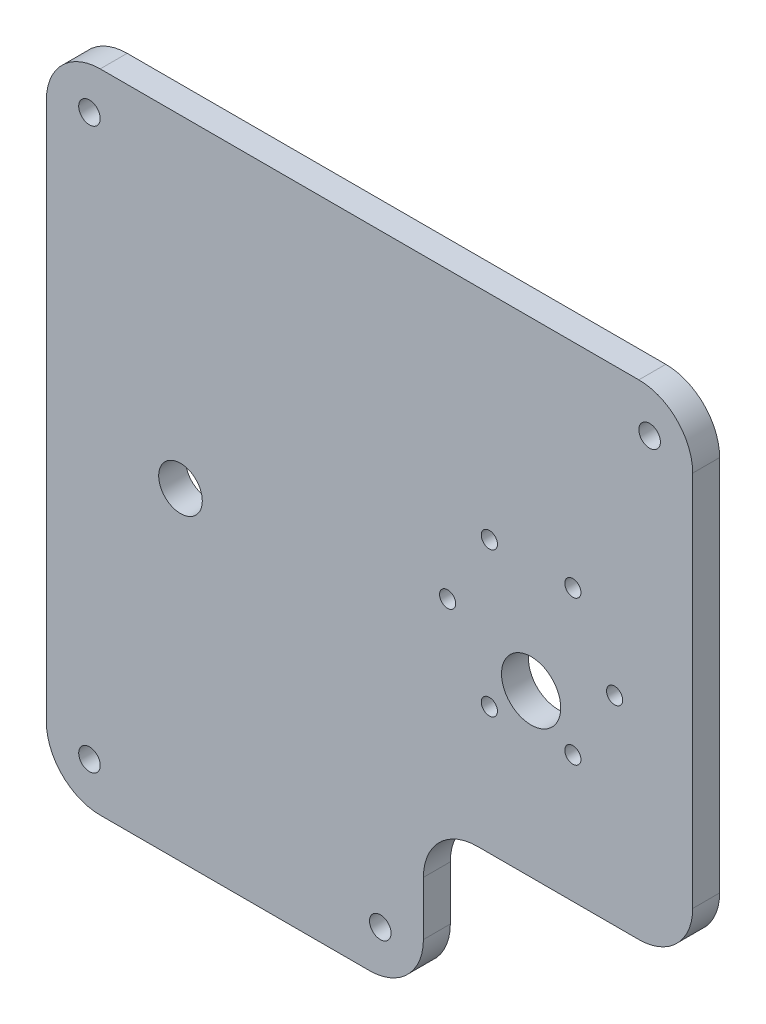
SolidWorks part; units mm, degrees
ref_plane "Alzado" through (0, 0, 0) normal (0, 0, 1) x (1, 0, 0)
ref_plane "Planta" through (0, 0, 0) normal (0, 1, 0) x (1, 0, 0)
ref_plane "Vista lateral" through (0, 0, 0) normal (1, 0, 0) x (0, 0, -1)
sketch "Croquis1" plane through (0, 0, 0) normal (0, 0, 1) x (1, 0, 0)
  line L0 (110, 30) -> (80, 30)
  line L1 (10, 0) -> (60, 0)
  line L2 (0, 10) -> (0, 110)
  line L3 (10, 120) -> (110, 120)
  line L4 (120, 40) -> (120, 110)
  line L5 (70, 20) -> (70, 10)
  arc A0 (10, 0) -> (0, 10) centre (10, 10) cw
  arc A1 (70, 10) -> (60, 0) centre (60, 10) cw
  arc A2 (110, 120) -> (120, 110) centre (110, 110) cw
  arc A3 (0, 110) -> (10, 120) centre (10, 110) cw
  arc A4 (80, 30) -> (70, 20) centre (80, 20) ccw
  arc A5 (110, 30) -> (120, 40) centre (110, 40) ccw
  point P7 (0, 0)
  point P10 (120, 0)
  point P15 (0, 120)
  dimension "D3" = 10
  dimension "D6" = 10
  dimension "D1" = 120
  dimension "D2" = 120
  dimension "D4" = 30
  dimension "D5" = 50
extrude "Saliente-Extruir1" add sketch "Croquis1" along normal blind 5
sketch "Croquis2" plane through (0, 0, 5) normal (0, 0, 1) x (1, 0, 0)
  line L0 (60, 120) -> (60, 75.4201) construction
  line L1 (110, 120) -> (10, 120) construction
  line L2 (0, 110) -> (0, 10) construction
  line L3 (0, 60) -> (90, 60) construction
  line L4 (120, 40) -> (120, 110) construction
  line L5 (70, 10) -> (70, 20) construction
  line L6 (10, 0) -> (60, 0) construction
  line L9 (90, 67) -> (90, 60) construction
  line L10 (82.25, 80.4234) -> (97.75, 53.5766) construction
  line L11 (97.75, 80.4234) -> (82.25, 53.5766) construction
  line L12 (74.5, 67) -> (105.5, 67) construction
  circle A0 centre (8, 112) radius 2
  circle A1 centre (8, 8) radius 2
  circle A2 centre (112, 8) radius 2
  circle A3 centre (112, 112) radius 2
  circle A5 centre (62, 8) radius 2
  circle A6 centre (24.9, 60) radius 4.05
  circle A8 centre (82.25, 80.4234) radius 1.5
  circle A9 centre (97.75, 80.4234) radius 1.5
  circle A10 centre (105.5, 67) radius 1.5
  circle A11 centre (97.75, 53.5766) radius 1.5
  circle A12 centre (82.25, 53.5766) radius 1.5
  circle A13 centre (74.5, 67) radius 1.5
  circle A15 centre (90, 60) radius 5.5
  circle A16 centre (90, 67) radius 15.5 construction
  point P23 (70, 15)
  dimension "D3" = 4
  dimension "D6" = 4
  dimension "D9" = 8.1
  dimension "D13" = 7
  dimension "D14" = 31
  dimension "D17" = 60
  dimension "D18" = 60
  dimension "D15" = 3
  dimension "D16" = 11
  dimension "D1" = 8
  dimension "D2" = 8
  dimension "D5" = 30
  dimension "D7" = 8
  dimension "D8" = 8
  dimension "D10" = 65.1
extrude "Cortar-Extruir1" cut sketch "Croquis2" against normal blind 10
sketch "Croquis3" plane through (0, 0, 5) normal (0, 0, 1) x (1, 0, 0)
  line L6 (70, 10) -> (70, 20)
  line L7 (80, 30) -> (110, 30)
  line L8 (120, 40) -> (120, 110)
  line L9 (110, 120) -> (10, 120)
  line L10 (0, 110) -> (0, 10)
  line L11 (10, 0) -> (60, 0)
  line L12 (70, 10) -> (70, 20)
  line L13 (80, 30) -> (110, 30)
  line L14 (120, 40) -> (120, 110)
  line L15 (110, 120) -> (10, 120)
  line L16 (0, 110) -> (0, 10)
  line L17 (10, 0) -> (60, 0)
  circle A0 centre (74.5, 67) radius 1.5 construction
  circle A1 centre (82.25, 80.4234) radius 1.5 construction
  circle A2 centre (97.75, 80.4234) radius 1.5 construction
  circle A3 centre (105.5, 67) radius 1.5 construction
  circle A4 centre (97.75, 53.5766) radius 1.5 construction
  circle A5 centre (82.25, 53.5766) radius 1.5 construction
  arc A6 (60, 0) -> (70, 10) centre (60, 10) ccw
  arc A7 (80, 30) -> (70, 20) centre (80, 20) ccw
  arc A8 (110, 30) -> (120, 40) centre (110, 40) ccw
  arc A9 (120, 110) -> (110, 120) centre (110, 110) ccw
  arc A10 (10, 120) -> (0, 110) centre (10, 110) ccw
  arc A11 (0, 10) -> (10, 0) centre (10, 10) ccw
  arc A12 (60, 0) -> (70, 10) centre (60, 10) ccw
  arc A13 (80, 30) -> (70, 20) centre (80, 20) ccw
  arc A14 (110, 30) -> (120, 40) centre (110, 40) ccw
  arc A15 (120, 110) -> (110, 120) centre (110, 110) ccw
  arc A16 (10, 120) -> (0, 110) centre (10, 110) ccw
  arc A17 (0, 10) -> (10, 0) centre (10, 10) ccw
  circle A18 centre (62, 8) radius 2 construction
  circle A19 centre (8, 8) radius 2 construction
  circle A20 centre (112, 112) radius 2 construction
  circle A21 centre (90, 60) radius 5.5 construction
  circle A22 centre (24.9, 60) radius 4.05 construction
  circle A23 centre (8, 112) radius 2 construction
  circle A24 centre (74.5, 67) radius 1.5
  circle A25 centre (82.25, 80.4234) radius 1.5
  circle A26 centre (97.75, 80.4234) radius 1.5
  circle A27 centre (105.5, 67) radius 1.5
  circle A28 centre (97.75, 53.5766) radius 1.5
  circle A29 centre (82.25, 53.5766) radius 1.5
  circle A30 centre (62, 8) radius 2
  circle A31 centre (8, 8) radius 2
  circle A32 centre (112, 112) radius 2
  circle A33 centre (90, 60) radius 5.5
  circle A34 centre (24.9, 60) radius 4.05
  circle A35 centre (8, 112) radius 2
  dimension "D1" = 0
